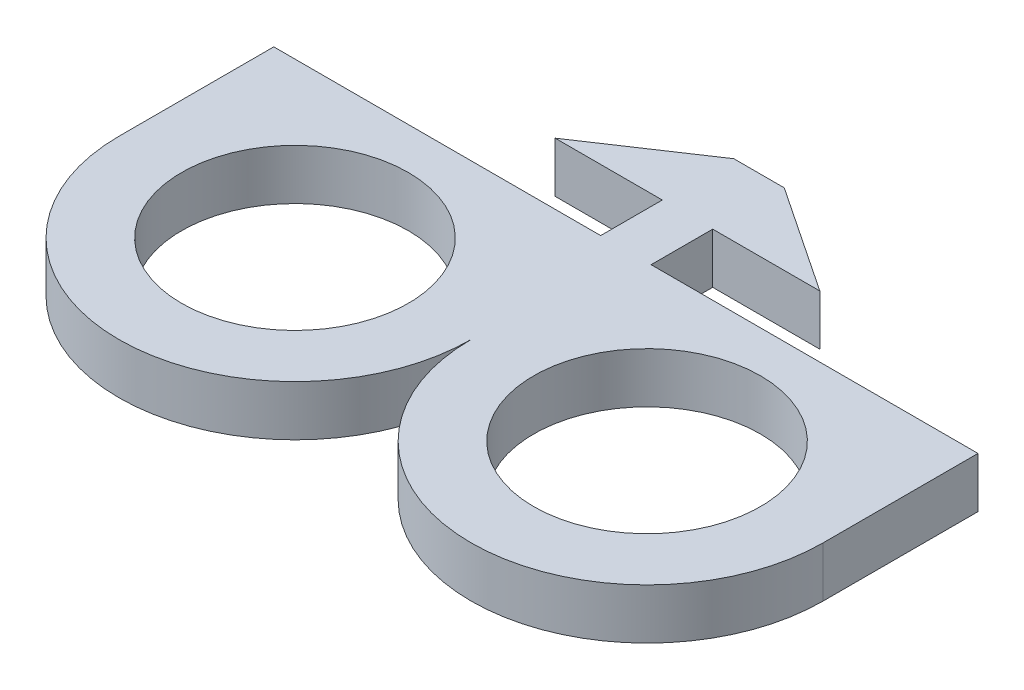
SolidWorks part; units mm, degrees
ref_plane "Front" through (0, 0, 0) normal (0, 0, 1) x (1, 0, 0)
ref_plane "Top" through (0, 0, 0) normal (0, 1, 0) x (1, 0, 0)
ref_plane "Right" through (0, 0, 0) normal (1, 0, 0) x (0, 0, -1)
sketch "Sketch1" plane through (0, 0, 0) normal (0, 1, 0) x (1, 0, 0)
  line L0 (-1.7907, 2.1875) -> (-9.398, 2.1875)
  line L2 (-1.7907, -2.1875) -> (-1.7907, 2.1875)
  line L4 (1.7907, -2.1875) -> (1.7907, 2.1875)
  line L7 (-9.398, 2.1875) -> (-1.7907, 7.2675)
  line L8 (-1.7907, 7.2675) -> (1.7907, 7.2675)
  line L9 (1.7907, 7.2675) -> (9.398, 2.1875)
  line L10 (9.398, 2.1875) -> (1.7907, 2.1875)
  line L11 (1.7907, -2.1875) -> (25.0063, -2.1875)
  line L12 (-1.7907, -2.1875) -> (-25.0063, -2.1875)
  line L13 (-25.0063, -2.1875) -> (-25.0063, -13.1857)
  line L14 (-25.0063, -13.1857) -> (25.0063, -13.1857)
  line L15 (25.0063, -13.1857) -> (25.0063, -2.1875)
  line L16 (25.0063, -2.1875) -> (1.7907, -2.1875)
  point P0 (0, 0)
  point P17 (0, 7.2675)
  point P19 (0, -13.1857)
  point P24 (1.7907, 0)
  dimension "D1" = 18.796
  dimension "D2" = 3.5814
  dimension "D3" = 50.0126
  dimension "D4" = 10.9982
  dimension "D5" = 5.08
  dimension "D7" = 4.375
extrude "Boss-Extrude1" add sketch "Sketch1" along normal blind 3.5814 contours L14 L15 L11 L4 L10 L9 L8 L7 L0 L2 L12 L13
sketch "Sketch3" plane through (0, 3.5814, 0) normal (0, 1, 0) x (1, 0, 0)
  line L3 (-25.0063, -13.1857) -> (25.0063, -13.1857) construction
  line L16 (-25.0063, -13.1857) -> (25.0063, -13.1857)
  line L17 (25.0063, -13.1857) -> (25.0063, -2.1875)
  line L18 (25.0063, -2.1875) -> (1.7907, -2.1875)
  line L19 (1.7907, -2.1875) -> (1.7907, 2.1875)
  line L20 (1.7907, 2.1875) -> (9.398, 2.1875)
  line L21 (9.398, 2.1875) -> (1.7907, 7.2675)
  line L22 (1.7907, 7.2675) -> (-1.7907, 7.2675)
  line L23 (-1.7907, 7.2675) -> (-9.398, 2.1875)
  line L24 (-9.398, 2.1875) -> (-1.7907, 2.1875)
  line L25 (-1.7907, 2.1875) -> (-1.7907, -2.1875)
  line L26 (-1.7907, -2.1875) -> (-25.0063, -2.1875)
  line L27 (-25.0063, -2.1875) -> (-25.0063, -13.1857)
  line L28 (-25.0063, -13.1857) -> (25.0063, -13.1857)
  arc A2 (-25.0063, -13.1857) -> (0, -13.1857) centre (-12.5031, -13.1857) ccw
  arc A3 (0, -13.1857) -> (25.0063, -13.1857) centre (12.5032, -13.1857) ccw
  point P7 (0, 0)
  line M15 (-25.0063, -13.1857) -> (25.0063, -13.1857)
  dimension "D1" = 0
extrude "Boss-Extrude2" add sketch "Sketch3" against normal up to surface (3.5814 mm away) contours A2 M15 | L28 A3 up to face at (0, 0, 0.9864)
sketch "Sketch4" plane through (0, 3.5814, 0) normal (0, 1, 0) x (1, 0, 0)
  circle A0 centre (-12.5031, -13.1857) radius 8.0518
  circle A1 centre (12.5032, -13.1857) radius 8.0518
  arc A2 (-25.0063, -13.1857) -> (0, -13.1857) centre (-12.5031, -13.1857) ccw construction
  arc A3 (0, -13.1857) -> (25.0063, -13.1857) centre (12.5032, -13.1857) ccw construction
  dimension "D1" = 16.1036
extrude "Cut-Extrude2" cut sketch "Sketch4" against normal through all
